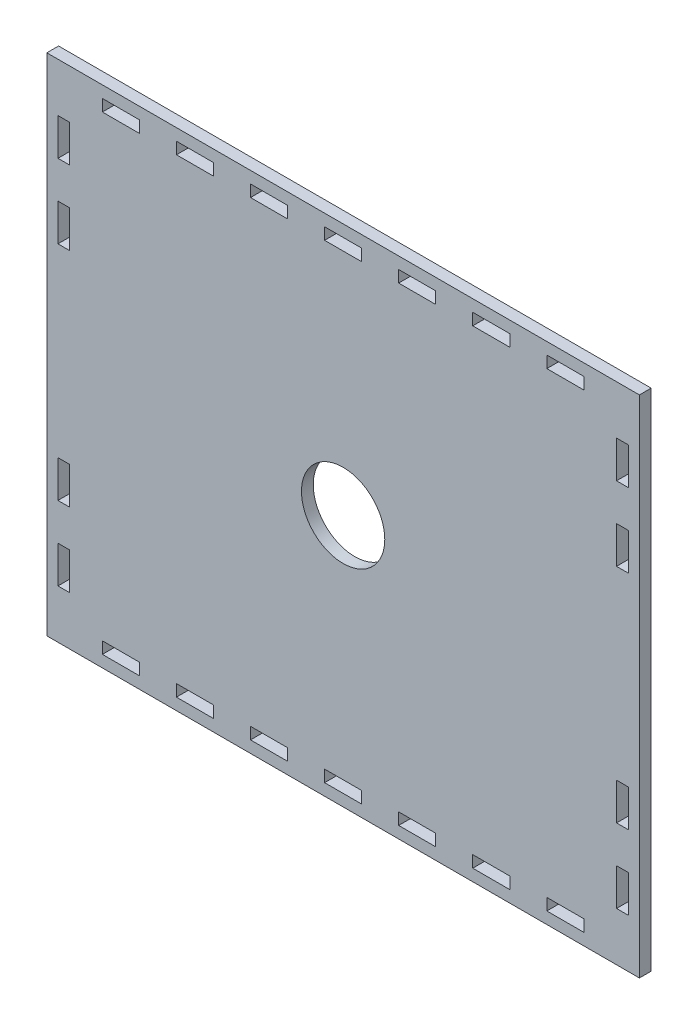
SolidWorks part; units mm, degrees
ref_plane "Front Plane" through (0, 0, 0) normal (0, 0, 1) x (1, 0, 0)
ref_plane "Top Plane" through (0, 0, 0) normal (0, 1, 0) x (1, 0, 0)
ref_plane "Right Plane" through (0, 0, 0) normal (1, 0, 0) x (0, 0, -1)
sketch "Sketch1" plane through (0, 0, 0) normal (0, 0, 1) x (1, 0, 0)
  line L0 (35, 133.07) -> (45, 133.07)
  line L1 (0, -0.105) -> (160, -0.105)
  line L2 (0, -0.105) -> (0, 136.245)
  line L3 (0, 136.245) -> (160, 136.245)
  line L4 (160, -0.105) -> (160, 136.245)
  line L5 (15, 133.07) -> (25, 133.07)
  line L6 (15, 133.07) -> (15, 129.895)
  line L7 (15, 129.895) -> (25, 129.895)
  line L8 (25, 133.07) -> (25, 129.895)
  line L9 (35, 133.07) -> (35, 129.895)
  line L10 (35, 129.895) -> (45, 129.895)
  line L11 (45, 133.07) -> (45, 129.895)
  line L12 (55, 133.07) -> (65, 133.07)
  line L13 (55, 133.07) -> (55, 129.895)
  line L14 (55, 129.895) -> (65, 129.895)
  line L15 (65, 133.07) -> (65, 129.895)
  line L16 (75, 133.07) -> (85, 133.07)
  line L17 (75, 133.07) -> (75, 129.895)
  line L18 (75, 129.895) -> (85, 129.895)
  line L19 (85, 133.07) -> (85, 129.895)
  line L20 (95, 133.07) -> (105, 133.07)
  line L21 (95, 133.07) -> (95, 129.895)
  line L22 (95, 129.895) -> (105, 129.895)
  line L23 (105, 133.07) -> (105, 129.895)
  line L24 (115, 133.07) -> (125, 133.07)
  line L25 (115, 133.07) -> (115, 129.895)
  line L26 (115, 129.895) -> (125, 129.895)
  line L27 (125, 133.07) -> (125, 129.895)
  line L28 (135, 133.07) -> (145, 133.07)
  line L29 (135, 133.07) -> (135, 129.895)
  line L30 (135, 129.895) -> (145, 129.895)
  line L31 (145, 133.07) -> (145, 129.895)
  line L32 (0, 68.07) -> (152.2847, 68.07) construction
  line L33 (145, 3.07) -> (145, 6.245)
  line L34 (135, 6.245) -> (145, 6.245)
  line L35 (135, 3.07) -> (135, 6.245)
  line L36 (135, 3.07) -> (145, 3.07)
  line L37 (125, 3.07) -> (125, 6.245)
  line L38 (115, 6.245) -> (125, 6.245)
  line L39 (115, 3.07) -> (115, 6.245)
  line L40 (115, 3.07) -> (125, 3.07)
  line L41 (105, 3.07) -> (105, 6.245)
  line L42 (95, 6.245) -> (105, 6.245)
  line L43 (95, 3.07) -> (95, 6.245)
  line L44 (95, 3.07) -> (105, 3.07)
  line L45 (85, 3.07) -> (85, 6.245)
  line L46 (75, 6.245) -> (85, 6.245)
  line L47 (75, 3.07) -> (75, 6.245)
  line L48 (75, 3.07) -> (85, 3.07)
  line L49 (65, 3.07) -> (65, 6.245)
  line L50 (55, 6.245) -> (65, 6.245)
  line L51 (55, 3.07) -> (55, 6.245)
  line L52 (55, 3.07) -> (65, 3.07)
  line L53 (45, 3.07) -> (45, 6.245)
  line L54 (35, 6.245) -> (45, 6.245)
  line L55 (35, 3.07) -> (35, 6.245)
  line L56 (25, 3.07) -> (25, 6.245)
  line L57 (15, 6.245) -> (25, 6.245)
  line L58 (15, 3.07) -> (15, 6.245)
  line L59 (15, 3.07) -> (25, 3.07)
  line L60 (35, 3.07) -> (45, 3.07)
  line L61 (3, 43.07) -> (6.175, 43.07)
  line L62 (3, 103.07) -> (6.175, 103.07)
  line L63 (3, 123.07) -> (6.175, 123.07)
  line L64 (3, 123.07) -> (3, 113.07)
  line L65 (3, 113.07) -> (6.175, 113.07)
  line L66 (6.175, 123.07) -> (6.175, 113.07)
  line L67 (3, 103.07) -> (3, 93.07)
  line L68 (3, 93.07) -> (6.175, 93.07)
  line L69 (6.175, 103.07) -> (6.175, 93.07)
  line L70 (3, 43.07) -> (3, 33.07)
  line L71 (3, 33.07) -> (6.175, 33.07)
  line L72 (6.175, 43.07) -> (6.175, 33.07)
  line L73 (3, 23.07) -> (6.175, 23.07)
  line L74 (3, 23.07) -> (3, 13.07)
  line L75 (3, 13.07) -> (6.175, 13.07)
  line L76 (6.175, 23.07) -> (6.175, 13.07)
  line L77 (160, 136.245) -> (0, -0.105) construction
  line L78 (80, 67.5) -> (80, 90.9813) construction
  line L79 (153.825, 23.07) -> (153.825, 13.07)
  line L80 (157, 13.07) -> (153.825, 13.07)
  line L81 (157, 23.07) -> (157, 13.07)
  line L82 (157, 23.07) -> (153.825, 23.07)
  line L83 (153.825, 43.07) -> (153.825, 33.07)
  line L84 (157, 33.07) -> (153.825, 33.07)
  line L85 (157, 43.07) -> (157, 33.07)
  line L86 (157, 43.07) -> (153.825, 43.07)
  line L87 (153.825, 103.07) -> (153.825, 93.07)
  line L88 (157, 93.07) -> (153.825, 93.07)
  line L89 (157, 103.07) -> (157, 93.07)
  line L90 (153.825, 123.07) -> (153.825, 113.07)
  line L91 (157, 113.07) -> (153.825, 113.07)
  line L92 (157, 123.07) -> (157, 113.07)
  line L93 (157, 123.07) -> (153.825, 123.07)
  line L94 (157, 103.07) -> (153.825, 103.07)
  circle A0 centre (80, 68.07) radius 11.25
  dimension "D1" = 136.35
  dimension "D2" = 160
  dimension "D3" = 10
  dimension "D4" = 3.175
  dimension "D5" = 3.175
  dimension "D7" = 7
  dimension "D8" = 15
  dimension "D6" = 15
  dimension "D9" = 3.175
  dimension "D10" = 3
  dimension "D11" = 10
  dimension "D12" = 13.175
  dimension "D13" = 3.175
  dimension "D14" = 10
  dimension "D15" = 3
  dimension "D16" = 10
  dimension "D17" = 50
  dimension "D18" = 3
  dimension "D19" = 3.175
  dimension "D20" = 3
  dimension "D21" = 10
  dimension "D22" = 3.175
  dimension "D23" = 10
  dimension "D24" = 10
  dimension "D25" = 10
extrude "Boss-Extrude1" add sketch "Sketch1" along normal blind 3.175
